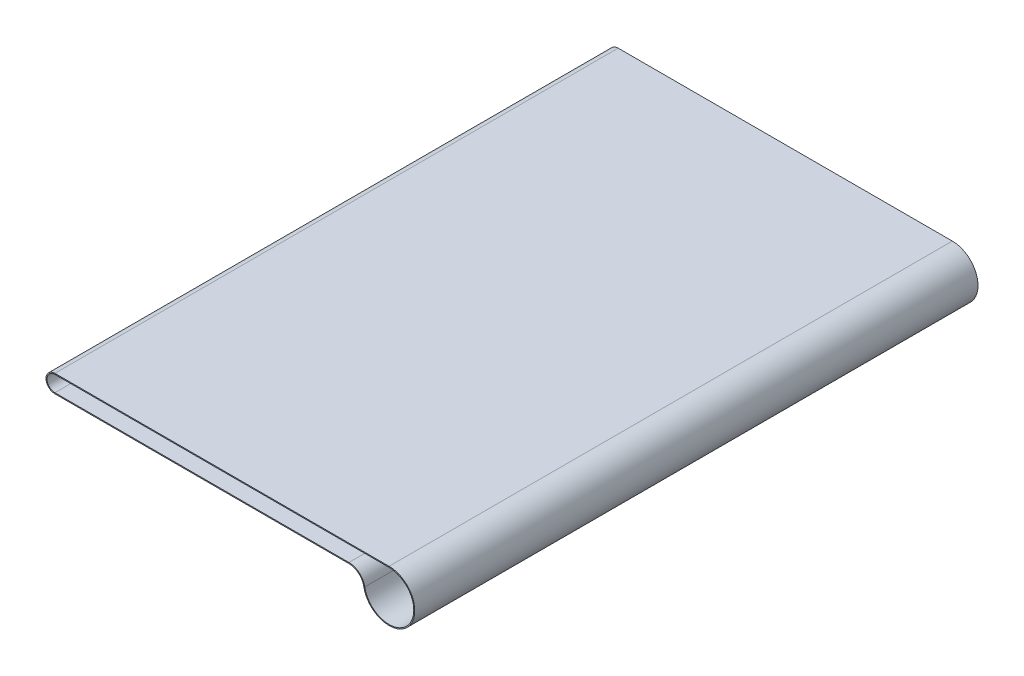
SolidWorks part; units mm, degrees
ref_plane "前视基准面" through (0, 0, 0) normal (0, 0, 1) x (1, 0, 0)
ref_plane "上视基准面" through (0, 0, 0) normal (0, 1, 0) x (1, 0, 0)
ref_plane "右视基准面" through (0, 0, 0) normal (1, 0, 0) x (0, 0, -1)
sketch "草图1" plane through (0, 0, 0) normal (0, 0, 1) x (1, 0, 0)
  line L0 (-54.5025, 0) -> (77.9283, 0) construction
  line L1 (-12.405, 0) -> (325.768, 0)
  line L3 (-12.405, 1) -> (325.768, 1)
  line L5 (-12.405, -16) -> (285.1237, -16)
  line L6 (-12.405, -17) -> (285.1237, -17)
  arc A0 (-12.405, 0) -> (-12.405, -16) centre (-12.405, -8) ccw
  arc A1 (301.1611, -29.4157) -> (325.768, 0) centre (325.768, -25) ccw
  arc A2 (-12.405, 1) -> (-12.405, -17) centre (-12.405, -8) ccw
  arc A3 (300.1768, -29.5923) -> (325.768, 1) centre (325.768, -25) ccw
  arc A4 (301.1611, -29.4157) -> (285.1237, -16) centre (285.1237, -32.2936) ccw
  arc A5 (300.1768, -29.5923) -> (285.1237, -17) centre (285.1237, -32.2936) ccw
  point P18 (300.144, -29.4157)
  point P20 (284.3819, -33.0625)
  dimension "D1" = 16
  dimension "D2" = 50
  dimension "D4" = 18
  dimension "D5" = 52
  dimension "D3" = 338.6
extrude "凸台-拉伸1" add sketch "草图1" along normal blind 570
